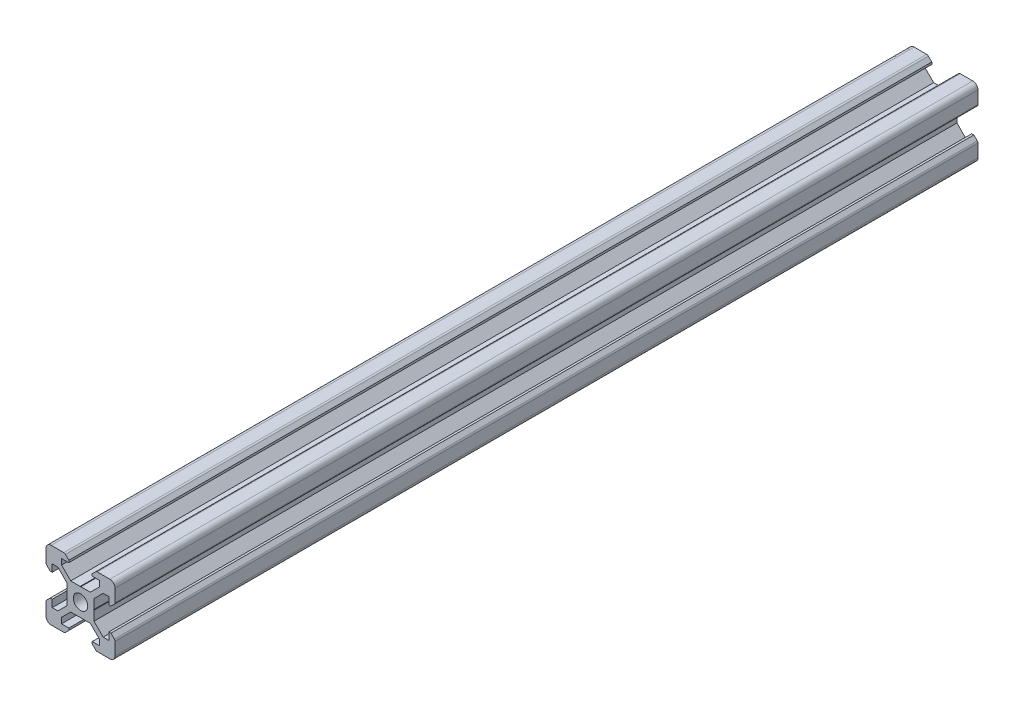
SolidWorks part; units mm, degrees
ref_plane "Front" through (0, 0, 0) normal (0, 0, 1) x (1, 0, 0)
ref_plane "Top" through (0, 0, 0) normal (0, 1, 0) x (1, 0, 0)
ref_plane "Right" through (0, 0, 0) normal (1, 0, 0) x (0, 0, -1)
sketch "Sketch1" plane through (0, 0, 0) normal (0, 0, 1) x (1, 0, 0)
  line L0 (-8.5, 10) -> (-10, 8.5) construction
  line L1 (-8.5, 10) -> (-4.8628, 10)
  line L2 (-10, 8.5) -> (-10, 4.8628)
  line L3 (-8.5, -10) -> (-4.8628, -10)
  line L4 (10, 8.5) -> (10, 4.8628)
  line L5 (-10, 10) -> (10, -10) construction
  line L6 (-10, -10) -> (10, 10) construction
  line L7 (-5.5, -8.2) -> (-3.3865, -8.2)
  line L8 (-8.2, -5.5) -> (-8.2, -3.3865)
  line L9 (-5.5, 8.2) -> (-3.3865, 8.2)
  line L10 (8.2, -5.5) -> (8.2, -3.3865)
  line L11 (-3.9005, 2.8395) -> (-6.561, 5.5)
  line L12 (-6.561, 5.5) -> (-8.2, 5.5)
  line L13 (-2.8395, -3.9005) -> (-0.1, -3.9005)
  line L14 (-3.9005, -2.8395) -> (-3.9005, -0.1)
  line L15 (-2.8395, 3.9005) -> (-0.1, 3.9005)
  line L16 (3.9005, -2.8395) -> (3.9005, -0.1)
  line L17 (-8.2, 3.3865) -> (-8.81, 3.3865)
  line L18 (-8.81, 3.3865) -> (-9.7976, 4.3741)
  line L19 (8.5, 10) -> (10, 8.5) construction
  line L20 (-2.8395, 3.9005) -> (-5.5, 6.561)
  line L21 (-5.5, 6.561) -> (-5.5, 8.2)
  line L22 (-3.3865, 8.2) -> (-3.3865, 8.81)
  line L23 (-3.3865, 8.81) -> (-4.3741, 9.7976)
  line L24 (0, 24.069) -> (0, -33.8154) construction
  line L25 (3.3865, 8.81) -> (4.3741, 9.7976)
  line L26 (3.3865, 8.2) -> (3.3865, 8.81)
  line L27 (5.5, 6.561) -> (5.5, 8.2)
  line L28 (2.8395, 3.9005) -> (5.5, 6.561)
  line L29 (3.3865, 8.2) -> (5.5, 8.2)
  line L30 (4.8628, 10) -> (8.5, 10)
  line L31 (-0.1, 3.9005) -> (0, 3.8005)
  line L32 (0.1, 3.9005) -> (0, 3.8005)
  line L33 (0.1, 3.9005) -> (2.8395, 3.9005)
  line L34 (25.9287, 0) -> (-28.3459, 0) construction
  line L35 (-0.1, -3.9005) -> (0, -3.8005)
  line L36 (0.1, -3.9005) -> (0, -3.8005)
  line L37 (0.1, -3.9005) -> (2.8395, -3.9005)
  line L38 (-3.9005, 0.1) -> (-3.8005, 0)
  line L39 (-3.8005, 0) -> (-3.9005, -0.1)
  line L40 (-3.9005, 0.1) -> (-3.9005, 2.8395)
  line L41 (3.9005, 0.1) -> (3.8005, 0)
  line L42 (3.8005, 0) -> (3.9005, -0.1)
  line L43 (3.9005, 0.1) -> (3.9005, 2.8395)
  line L44 (8.81, 3.3865) -> (9.7976, 4.3741)
  line L45 (8.2, 3.3865) -> (8.81, 3.3865)
  line L46 (6.561, 5.5) -> (8.2, 5.5)
  line L47 (3.9005, 2.8395) -> (6.561, 5.5)
  line L48 (2.8395, -3.9005) -> (5.5, -6.561)
  line L49 (3.9005, -2.8395) -> (6.561, -5.5)
  line L50 (-2.8395, -3.9005) -> (-5.5, -6.561)
  line L51 (-3.9005, -2.8395) -> (-6.561, -5.5)
  line L52 (6.561, -5.5) -> (8.2, -5.5)
  line L53 (-6.561, -5.5) -> (-8.2, -5.5)
  line L54 (-8.81, -3.3865) -> (-9.7976, -4.3741)
  line L55 (-8.2, -3.3865) -> (-8.81, -3.3865)
  line L56 (8.81, -3.3865) -> (9.7976, -4.3741)
  line L57 (8.2, -3.3865) -> (8.81, -3.3865)
  line L58 (8.2, 3.3865) -> (8.2, 5.5)
  line L59 (10, -4.8628) -> (10, -8.5)
  line L60 (-8.2, 3.3865) -> (-8.2, 5.5)
  line L61 (-10, -4.8628) -> (-10, -8.5)
  line L62 (-3.3865, -8.81) -> (-4.3741, -9.7976)
  line L63 (-3.3865, -8.2) -> (-3.3865, -8.81)
  line L64 (3.3865, -8.81) -> (4.3741, -9.7976)
  line L65 (3.3865, -8.2) -> (3.3865, -8.81)
  line L66 (-5.5, -6.561) -> (-5.5, -8.2)
  line L67 (5.5, -6.561) -> (5.5, -8.2)
  line L68 (3.3865, -8.2) -> (5.5, -8.2)
  line L69 (4.8628, -10) -> (8.5, -10)
  circle A0 centre (0, 0) radius 2.1
  arc A1 (-8.5, 10) -> (-10, 8.5) centre (-8.5, 8.5) ccw
  arc A2 (10, 8.5) -> (8.5, 10) centre (8.5, 8.5) ccw
  arc A3 (-4.3741, 9.7976) -> (-4.8628, 10) centre (-4.8628, 9.3088) ccw
  arc A4 (4.8628, 10) -> (4.3741, 9.7976) centre (4.8628, 9.3088) ccw
  arc A5 (-8.5, -10) -> (-10, -8.5) centre (-8.5, -8.5) cw
  arc A6 (9.7976, 4.3741) -> (10, 4.8628) centre (9.3088, 4.8628) ccw
  arc A7 (-10, 4.8628) -> (-9.7976, 4.3741) centre (-9.3088, 4.8628) ccw
  arc A8 (-10, -4.8628) -> (-9.7976, -4.3741) centre (-9.3088, -4.8628) cw
  arc A9 (9.7976, -4.3741) -> (10, -4.8628) centre (9.3088, -4.8628) cw
  arc A10 (10, -8.5) -> (8.5, -10) centre (8.5, -8.5) cw
  arc A11 (-4.3741, -9.7976) -> (-4.8628, -10) centre (-4.8628, -9.3088) cw
  arc A12 (4.8628, -10) -> (4.3741, -9.7976) centre (4.8628, -9.3088) cw
  point P17 (-9.25, 9.25)
  point P21 (9.25, 9.25)
  dimension "D2" = 4.2
  dimension "D4" = 1.5
  dimension "D3" = 20
  dimension "D5" = 0.529
  dimension "D6" = 6.773
  dimension "D7" = 90
  dimension "D8" = 11
  dimension "D9" = 0.61
  dimension "D10" = 0.1
  dimension "D11" = 0.1
  dimension "D12" = 0.1
  dimension "D13" = 0.1
  dimension "D14" = 5.679
  dimension "D15" = 1.639
  dimension "D16" = 1.8
  dimension "D17" = 90
  dimension "D18" = 6.773
  dimension "D19" = 90
extrude "Boss-Extrude1" add sketch "Sketch1" along normal blind 250
